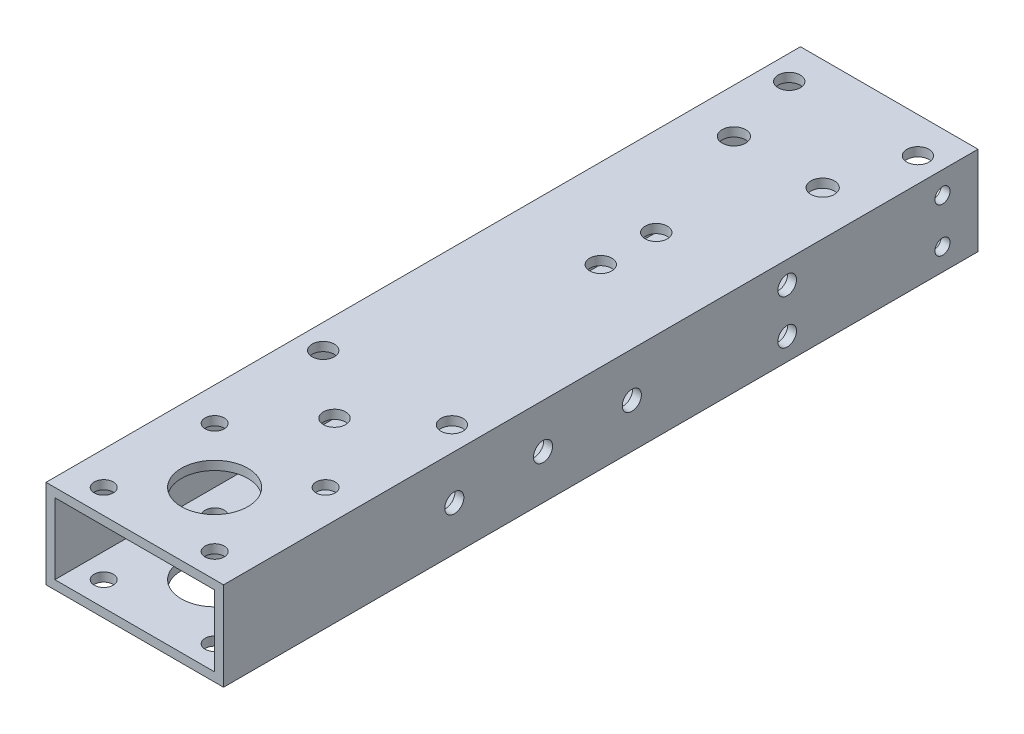
SolidWorks part; units mm, degrees
material "6061 合金"
ref_plane "前视基准面" through (0, 0, 0) normal (0, 0, 1) x (1, 0, 0)
ref_plane "上视基准面" through (0, 0, 0) normal (0, 1, 0) x (1, 0, 0)
ref_plane "右视基准面" through (0, 0, 0) normal (1, 0, 0) x (0, 0, -1)
sketch "草图1" plane through (0, 0, 0) normal (0, 0, 1) x (1, 0, 0)
  line L1 (-20, 10) -> (20, 10)
  line L2 (-20, 10) -> (-20, -10)
  line L3 (-20, -10) -> (20, -10)
  line L4 (20, 10) -> (20, -10)
  line L5 (-20, 10) -> (20, -10) construction
  line L6 (-20, -10) -> (20, 10) construction
  point P0 (0, 0)
  dimension "D1" = 40
  dimension "D2" = 20
extrude "拉伸-薄壁1" add sketch "草图1" along normal blind 190 thin
sketch "草图2" plane through (0, 10, 0) normal (0, 1, 0) x (1, 0, 0)
  line L0 (0, -190) -> (0, 0) construction
  line L1 (20, -190) -> (-20, -190) construction
  circle A0 centre (0, -180) radius 2.15
  circle A1 centre (0, -170) radius 2.15
  circle A2 centre (0, -160) radius 2.15
  dimension "D1" = 4.3
  dimension "D3" = 10
  dimension "D4" = 10
  dimension "D2" = 10
extrude "切除-拉伸1" [suppressed] cut sketch "草图2" against normal through all
sketch "草图3" plane through (0, 10, 0) normal (0, 1, 0) x (1, 0, 0)
  line L0 (0, -190) -> (0, 0) construction
  line L1 (20, -190) -> (-20, -190) construction
  line L3 (-12.5, -184.5) -> (12.5, -184.5) construction
  line L4 (-12.5, -184.5) -> (-12.5, -159.5) construction
  line L5 (-12.5, -159.5) -> (12.5, -159.5) construction
  line L6 (12.5, -184.5) -> (12.5, -159.5) construction
  line L7 (-12.5, -184.5) -> (12.5, -159.5) construction
  line L8 (-12.5, -159.5) -> (12.5, -184.5) construction
  circle A0 centre (-12.5, -184.5) radius 2.15
  circle A1 centre (-12.5, -159.5) radius 2.15
  circle A2 centre (12.5, -159.5) radius 2.15
  circle A3 centre (12.5, -184.5) radius 2.15
  circle A4 centre (0, -172) radius 7.5
  point P5 (0, -172)
  dimension "D4" = 4.3
  dimension "D5" = 15
  dimension "D1" = 18
  dimension "D2" = 25
  dimension "D3" = 25
extrude "切除-拉伸2" cut sketch "草图3" against normal through all
sketch "草图4" plane through (20, 0, 0) normal (1, 0, 0) x (0, 0, -1)
  line L5 (0, 0) -> (-30.369, 0) construction
  line L12 (0, -10) -> (0, 10) construction
  line L13 (-190, -10) -> (0, -10) construction
  line L15 (-190, 10) -> (0, 10) construction
  line L16 (-20, -10) -> (0, -10)
  line L17 (0, -10) -> (0, 10)
  line L18 (-20, 10) -> (0, 10)
  line L19 (-20, -10) -> (-20, 10)
  dimension "D1" = 20
extrude "切除-拉伸3" cut sketch "草图4" against normal through all
sketch "草图5" plane through (0, 10, 0) normal (0, 1, 0) x (1, 0, 0)
  line L0 (0, -190) -> (0, 25.9023) construction
  line L1 (20, -190) -> (-20, -190) construction
  circle A0 centre (0, -145) radius 2.5
  circle A1 centre (0, -85) radius 2.5
  circle A2 centre (0, -72.5) radius 2.5
  dimension "D1" = 5
  dimension "D2" = 60
  dimension "D4" = 12.5
  dimension "D3" = 45
extrude "切除-拉伸4" cut sketch "草图5" against normal through all
sketch "草图6" plane through (0, 10, 0) normal (0, 1, 0) x (1, 0, 0)
  line L0 (0, -190) -> (0, 11.0162) construction
  line L1 (20, -190) -> (-20, -190) construction
  line L3 (14.5, -133.0385) -> (-14.5, -133.0385) construction
  line L4 (14.5, -133.0385) -> (14.5, -28.0385) construction
  line L5 (14.5, -28.0385) -> (-14.5, -28.0385) construction
  line L6 (-14.5, -133.0385) -> (-14.5, -28.0385) construction
  line L7 (14.5, -133.0385) -> (-14.5, -28.0385) construction
  line L8 (14.5, -28.0385) -> (-14.5, -133.0385) construction
  circle A0 centre (-14.5, -133.0385) radius 2.5
  circle A1 centre (14.5, -133.0385) radius 2.5
  circle A2 centre (14.5, -28.0385) radius 2.5
  circle A3 centre (-14.5, -28.0385) radius 2.5
  point P5 (0, -80.5385)
  dimension "D1" = 5
  dimension "D2" = 29
  dimension "D3" = 105
  dimension "D4" = 56.9615
extrude "切除-拉伸5" cut sketch "草图6" against normal through all
sketch "草图7" plane through (0, -10, 0) normal (0, -1, 0) x (1, 0, 0)
  line L0 (0, 190) -> (0, 0) construction
  line L1 (-20, 190) -> (20, 190) construction
  circle A0 centre (-10, 45) radius 2.65
  circle A1 centre (10, 45) radius 2.65
  dimension "D1" = 5.3
  dimension "D2" = 20
  dimension "D3" = 145
extrude "切除-拉伸6" cut sketch "草图7" against normal through all
sketch "草图8" plane through (20, 0, 0) normal (1, 0, 0) x (0, 0, -1)
  line L0 (-20, 0) -> (-51.6996, 0) construction
  line L1 (-20, 10) -> (-20, -10) construction
  line L2 (-28, 0) -> (-28, 5) construction
  circle A0 centre (-28, 5) radius 1.7
  circle A1 centre (-28, -5) radius 1.7
  dimension "D2" = 3.4
  dimension "D3" = 8
  dimension "D1" = 5
extrude "切除-拉伸7" cut sketch "草图8" against normal through all
sketch "草图9" plane through (-20, 0, 0) normal (-1, 0, 0) x (0, 0, 1)
  line L0 (20, 0) -> (190, 0) construction
  line L1 (20, 10) -> (20, -10) construction
  line L2 (190, 10) -> (190, -10) construction
  line L3 (63, -5) -> (63, 5) construction
  circle A0 centre (63, -5) radius 2.1
  circle A1 centre (28, -5) radius 1.7 construction
  circle A2 centre (63, 5) radius 2.1
  circle A3 centre (98, 0) radius 2.15
  circle A4 centre (118, 0) radius 2.15
  circle A5 centre (138, 0) radius 2.15
  dimension "D1" = 4.2
  dimension "D2" = 35
  dimension "D4" = 20
  dimension "D5" = 20
  dimension "D6" = 35
  dimension "D7" = 4.3
  dimension "D3" = 10
extrude "切除-拉伸8" cut sketch "草图9" against normal through all
